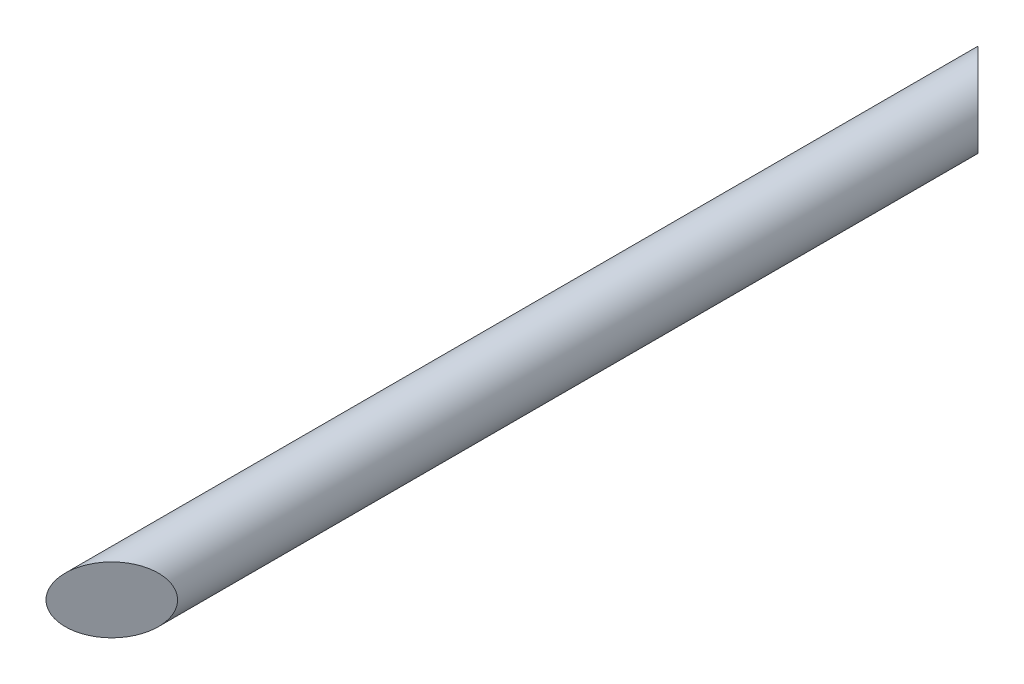
SolidWorks part; units mm, degrees
ref_plane "Front Plane" through (0, 0, 0) normal (0, 0, 1) x (1, 0, 0)
ref_plane "Top Plane" through (0, 0, 0) normal (0, 1, 0) x (1, 0, 0)
ref_plane "Right Plane" through (0, 0, 0) normal (1, 0, 0) x (0, 0, -1)
sketch "Sketch1" plane through (0, 0, 0) normal (0, 0, 1) x (1, 0, 0)
  circle A0 centre (0, 0) radius 30
  dimension "D1" = 60
extrude "Boss-Extrude2" add sketch "Sketch1" along normal blind 850 contours A0
ref_plane "Plane1" through (0, 40, 0) normal (0, 1, 0) x (1, 0, 0)
sketch "Sketch3" plane through (0, 40, 0) normal (0, 1, 0) x (1, 0, 0)
  line L0 (-30, 0) -> (30, -60)
  line L1 (30, -850) -> (30, 0) construction
  line L2 (30, -60) -> (30, 0)
  line L3 (30, 0) -> (-30, 0)
  dimension "D1" = 60
  dimension "D2" = 60
sketch "Sketch4" plane through (0, 40, 0) normal (0, 1, 0) x (1, 0, 0)
  line L0 (-30, -850) -> (30, -850)
  line L1 (30, -850) -> (30, -790)
  line L2 (30, -850) -> (30, 0) construction
  line L3 (30, -790) -> (-30, -850)
  dimension "D1" = 60
extrude "Cut-Extrude1" cut sketch "Sketch4" against normal blind 70
extrude "Cut-Extrude2" cut sketch "Sketch3" against normal blind 70 contours L3 L0 L2
